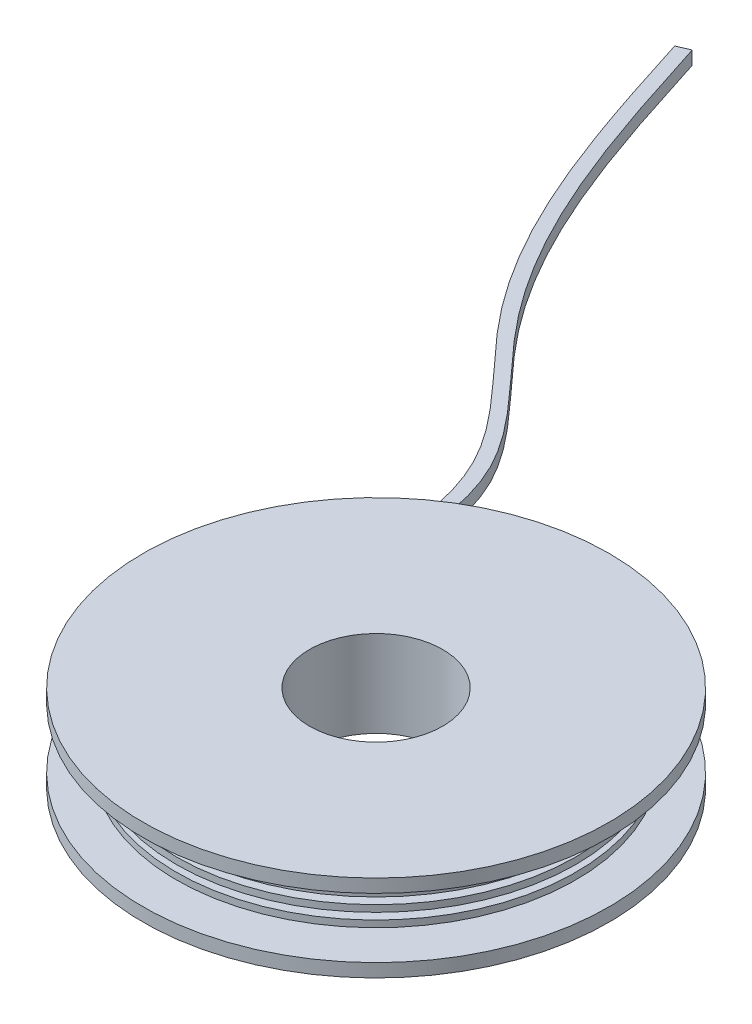
SolidWorks part; units mm, degrees
ref_plane "Ebene vorne" through (0, 0, 0) normal (0, 0, 1) x (1, 0, 0)
ref_plane "Ebene oben" through (0, 0, 0) normal (0, 1, 0) x (1, 0, 0)
ref_plane "Ebene rechts" through (0, 0, 0) normal (1, 0, 0) x (0, 0, -1)
sketch "Skizze2" plane through (0, 0, 0) normal (0, 0, 1) x (1, 0, 0)
  line L0 (0, 0) -> (0, 98.9218) construction
  line L1 (0, 0) -> (35, 0)
  line L2 (35, 0) -> (35, 2)
  line L3 (35, 2) -> (25, 2)
  line L4 (25, 2) -> (25, 3)
  line L5 (25, 3) -> (30, 3)
  line L6 (30, 3) -> (30, 4)
  line L7 (30, 4) -> (25, 4)
  line L8 (25, 4) -> (25, 5)
  line L9 (25, 5) -> (30, 5)
  line L10 (30, 5) -> (30, 6)
  line L11 (30, 6) -> (25, 6)
  line L12 (88.729, 6.5) -> (-42.4099, 6.5) construction
  line L13 (25, 6) -> (25, 7)
  line L14 (30, 7) -> (25, 7)
  line L15 (30, 8) -> (30, 7)
  line L16 (25, 8) -> (30, 8)
  line L17 (25, 9) -> (25, 8)
  line L18 (30, 9) -> (25, 9)
  line L19 (30, 10) -> (30, 9)
  line L20 (25, 10) -> (30, 10)
  line L21 (25, 11) -> (25, 10)
  line L22 (35, 11) -> (25, 11)
  line L23 (35, 13) -> (35, 11)
  line L24 (0, 13) -> (35, 13)
  line L25 (0, 0) -> (0, 13)
  point P19 (25, 6.5)
  dimension "D1" = 70
  dimension "D2" = 2
  dimension "D3" = 5
  dimension "D4" = 10
  dimension "D5" = 1
revolve "Rotation1" add sketch "Skizze2" angle 360 about L0
sketch "Skizze5" plane through (0, 3, 0) normal (0, -1, 0) x (1, 0, 0)
  line L0 (-27.3272, -12.3784) -> (-29.3272, -6.3179)
  line L1 (-70.0694, -114.9233) -> (-68.2349, -115.7201)
  circle A0 centre (0, 0) radius 30 construction
  spline S0 degree 3 poles (-27.3272, -12.3784) (-25.584, -25.0967) (-23.311, -45.1883) (-54.519, -72.5257) (-62.6677, -98.1877) (-68.2349, -115.7201) knots 0 0 0 0 0.308292 0.527424 1 1 1 1
  spline S1 degree 3 poles (-29.3272, -6.3179) (-27.3765, -20.5051) (-24.1795, -43.7557) (-56.295, -71.5733) (-64.4785, -97.3278) (-70.0694, -114.9233) knots 0 0 0 0 0.331505 0.543283 1 1 1 1
  dimension "D2" = 2
  dimension "D1" = 2
  dimension "D3" = 2
  dimension "D4" = 2
extrude "Linear austragen1" add sketch "Skizze5" along normal blind 1 and the other way blind 1
sketch "Skizze6" plane through (0, 13, 0) normal (0, 1, 0) x (1, 0, 0)
  circle A0 centre (0, 0) radius 10
  dimension "D1" = 20
extrude "Linear austragen2" cut sketch "Skizze6" against normal through all
